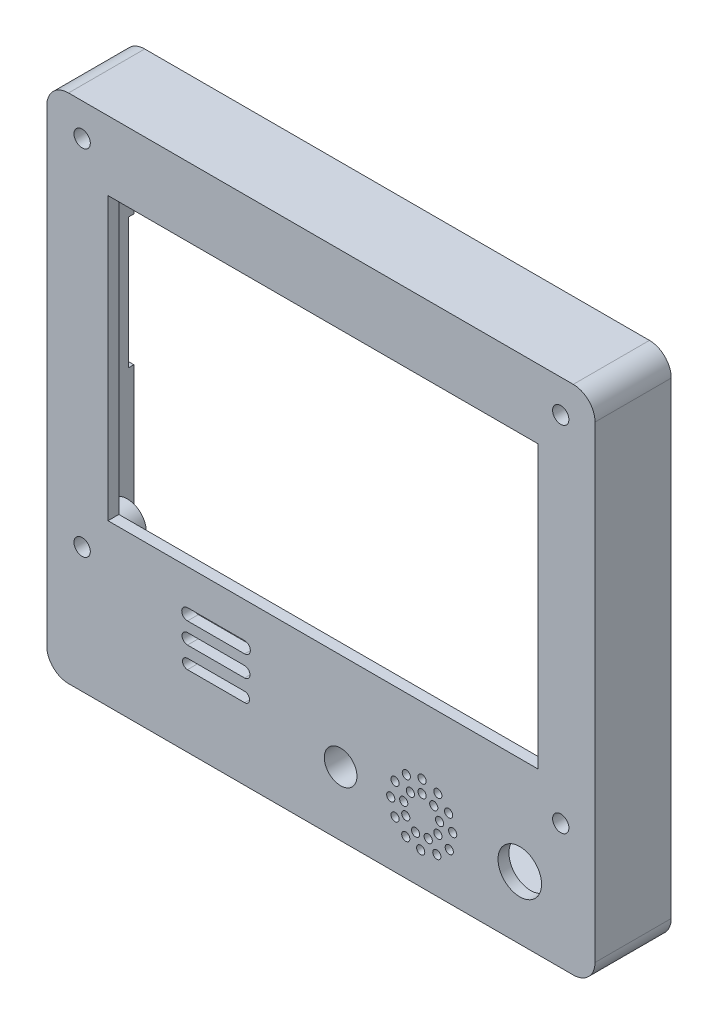
SolidWorks part; units mm, degrees
ref_plane "Front Plane" through (0, 0, 0) normal (0, 0, 1) x (1, 0, 0)
ref_plane "Top Plane" through (0, 0, 0) normal (0, 1, 0) x (1, 0, 0)
ref_plane "Right Plane" through (0, 0, 0) normal (1, 0, 0) x (0, 0, -1)
sketch "Sketch1" plane through (0, 0, 0) normal (0, 0, 1) x (1, 0, 0)
  line L0 (-18.9055, -35.0317) -> (-8.4055, -35.0317)
  line L1 (-44.7619, 35.9446) -> (55.9881, 35.9446)
  line L2 (-44.7619, 35.9446) -> (-44.7619, -58.0554)
  line L3 (-44.7619, -58.0554) -> (55.9881, -58.0554)
  line L4 (55.9881, 35.9446) -> (55.9881, -58.0554)
  line L5 (-18.9055, -37.1411) -> (-8.4055, -37.1411)
  line L6 (-18.9055, -39.0004) -> (-8.4055, -39.0004)
  line L7 (-18.9055, -40.9858) -> (-8.4055, -40.9858)
  line L8 (-18.9055, -43.0933) -> (-8.4055, -43.0933)
  line L9 (-18.9055, -44.9031) -> (-8.4055, -44.9031)
  circle A5 centre (42.1595, -46.5247) radius 4
  circle A6 centre (18.4475, -46.4785) radius 0.75
  circle A7 centre (19.2346, -43.5909) radius 0.75
  circle A8 centre (21.3068, -41.5066) radius 0.75
  circle A9 centre (24.2, -40.7566) radius 0.75
  circle A10 centre (27.1008, -41.5941) radius 0.75
  circle A11 centre (29.0793, -43.7304) radius 0.75
  circle A12 centre (26.3508, -43.9308) radius 0.75
  circle A13 centre (24.2, -43.0851) radius 0.75
  circle A14 centre (22.0568, -43.9308) radius 0.75
  circle A15 centre (20.8296, -45.9844) radius 0.75
  circle A16 centre (21.2089, -48.1001) radius 0.75
  circle A17 centre (23.0093, -49.8145) radius 0.75
  circle A18 centre (25.3319, -49.6608) radius 0.75
  circle A19 centre (27.1008, -48.1001) radius 0.75
  circle A20 centre (27.4256, -45.8986) radius 0.75
  circle A21 centre (29.8293, -46.4546) radius 0.75
  circle A22 centre (29.202, -49.4876) radius 0.75
  circle A23 centre (26.913, -51.4139) radius 0.75
  circle A24 centre (23.9495, -52.1639) radius 0.75
  circle A25 centre (21.2089, -51.4139) radius 0.75
  circle A26 centre (19.2346, -49.2822) radius 0.75
  arc A27 (-18.9055, -35.0317) -> (-18.9055, -37.1411) centre (-18.9055, -36.0864) ccw
  arc A28 (-8.4055, -37.1411) -> (-8.4055, -35.0317) centre (-8.4055, -36.0864) ccw
  arc A29 (-18.9055, -39.0004) -> (-18.9055, -40.9858) centre (-18.9055, -39.9931) ccw
  arc A30 (-8.4055, -40.9858) -> (-8.4055, -39.0004) centre (-8.4055, -39.9931) ccw
  arc A31 (-18.9055, -43.0933) -> (-18.9055, -44.9031) centre (-18.9055, -43.9982) ccw
  arc A32 (-8.4055, -44.9031) -> (-8.4055, -43.0933) centre (-8.4055, -43.9982) ccw
  dimension "D3" = 10.5
  dimension "D1" = 100.75
  dimension "D2" = 94
  dimension "D4" = 10.5
  dimension "D5" = 10.5
extrude "Boss-Extrude1" add sketch "Sketch1" along normal blind 14
sketch "Sketch2" plane through (0, 0, 0) normal (0, 0, -1) x (-1, 0, 0)
  line L1 (-53.9881, 33.9524) -> (42.7619, 33.9524)
  line L2 (-53.9881, 33.9524) -> (-53.9881, -56.0476)
  line L3 (-53.9881, -56.0476) -> (42.7619, -56.0476)
  line L4 (42.7619, 33.9524) -> (42.7619, -56.0476)
extrude "Cut-Extrude1" cut sketch "Sketch2" against normal blind 12
sketch "Sketch3" plane through (0, 0, 12) normal (0, 0, -1) x (-1, 0, 0)
  line L0 (44.7619, 35.9446) -> (44.7619, -58.0554) construction
  line L1 (-55.9881, 35.9446) -> (44.7619, 35.9446) construction
  line L2 (-55.9881, -58.0554) -> (-55.9881, 35.9446) construction
  line L3 (44.7619, -58.0554) -> (-55.9881, -58.0554) construction
  circle A0 centre (-49.4881, 29.9446) radius 3.549
  circle A1 centre (38.2619, 29.9446) radius 3.4088
  circle A2 centre (38.2619, -35.0554) radius 3.5
  circle A3 centre (-49.4881, -35.0554) radius 3.5
  dimension "D1" = 6.5
  dimension "D3" = 6.5
  dimension "D4" = 6
  dimension "D5" = 23
  dimension "D7" = 23
  dimension "D8" = 6.5
  dimension "D2" = 6
  dimension "D6" = 6.5
extrude "Boss-Extrude2" add sketch "Sketch3" along normal blind 6.3
sketch "Sketch4" plane through (0, 0, 12) normal (0, 0, -1) x (-1, 0, 0)
  line L0 (44.7619, -58.0554) -> (-55.9881, -58.0554) construction
  line L1 (44.7619, 35.9446) -> (44.7619, -58.0554) construction
  circle A0 centre (-9.2381, -46.3054) radius 4
  point P5 (-5.6131, -58.0554)
  dimension "D1" = 11.75
  dimension "D2" = 54
extrude "Boss-Extrude3" add sketch "Sketch4" along normal blind 6.3
sketch "Sketch7" plane through (0, 0, 5.7) normal (0, 0, -1) x (-1, 0, 0)
  circle A0 centre (-49.6837, 29.9289) radius 1.5
sketch "Sketch9" plane through (0, 0, 5.7) normal (0, 0, -1) x (-1, 0, 0)
  circle A0 centre (38.2619, 29.9446) radius 1.5
  circle A1 centre (38.2619, -35.0554) radius 1.5
sketch "Sketch10" plane through (0, 0, 5.7) normal (0, 0, -1) x (-1, 0, 0)
  circle A0 centre (-49.6869, -35.0598) radius 1.5
sketch "Sketch11" plane through (0, 0, 5.7) normal (0, 0, -1) x (-1, 0, 0)
  circle A0 centre (-9.2381, -46.3054) radius 3
extrude "Cut-Extrude2" cut sketch "Sketch7" against normal blind 10
extrude "Cut-Extrude3" cut sketch "Sketch11" against normal blind 10
extrude "Cut-Extrude4" cut sketch "Sketch10" against normal blind 10
extrude "Cut-Extrude5" cut sketch "Sketch9" against normal blind 10
sketch "Sketch12" plane through (0, 0, 12) normal (0, 0, -1) x (-1, 0, 0)
  line L1 (-45.4881, 23.2446) -> (33.5119, 23.2446)
  line L2 (-45.4881, 23.2446) -> (-45.4881, -28.5054)
  line L3 (-45.4881, -28.5054) -> (33.5119, -28.5054)
  line L4 (33.5119, 23.2446) -> (33.5119, -28.5054)
  line L5 (-55.9881, -58.0554) -> (-55.9881, 35.9446) construction
  line L7 (-55.9881, 35.9446) -> (44.7619, 35.9446) construction
  dimension "D1" = 79
  dimension "D2" = 51.75
  dimension "D3" = 10.5
  dimension "D4" = 12.7
extrude "Cut-Extrude6" cut sketch "Sketch12" against normal blind 6.3
fillet "Fillet1" radius 4 4 edges at (55.9881, 35.9446, 7) (55.9881, -58.0554, 7) (-44.7619, -58.0554, 7) (-44.7619, 35.9446, 7)
sketch "Sketch13" plane through (-44.7619, 0, 0) normal (-1, 0, 0) x (0, 0, 1)
  line L1 (0, 8.6946) -> (1, 8.6946)
  line L2 (0, 8.6946) -> (0, -15.3054)
  line L3 (0, -15.3054) -> (1, -15.3054)
  line L4 (1, 8.6946) -> (1, -15.3054)
  line L6 (0, 31.9446) -> (0, -54.0554) construction
  line L7 (14, 31.9446) -> (0, 31.9446) construction
  dimension "D1" = 1
  dimension "D2" = 24
  dimension "D3" = 23.25
extrude "Cut-Extrude7" cut sketch "Sketch13" against normal blind 3
